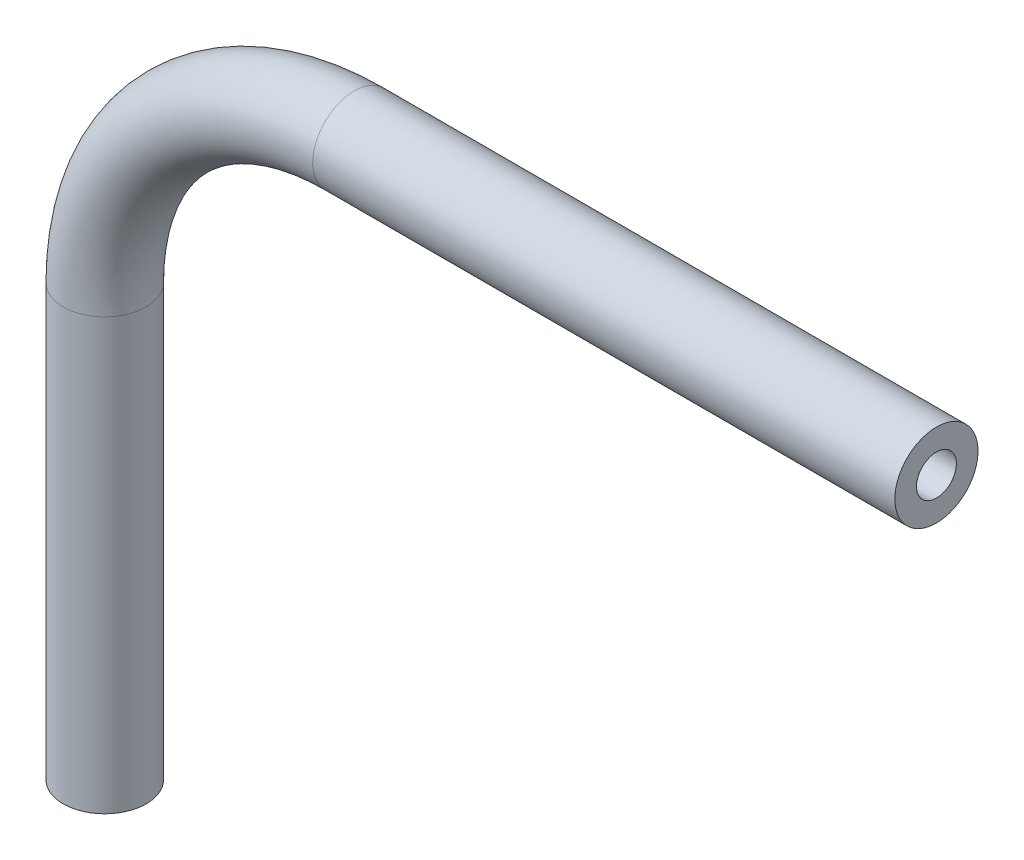
SolidWorks part; units mm, degrees
material "AISI Type 316L stainless steel"
ref_plane "Front Plane" through (0, 0, 0) normal (0, 0, 1) x (1, 0, 0)
ref_plane "Top Plane" through (0, 0, 0) normal (0, 1, 0) x (1, 0, 0)
ref_plane "Right Plane" through (0, 0, 0) normal (1, 0, 0) x (0, 0, -1)
sketch "Sketch1" plane through (0, 0, 0) normal (0, 0, 1) x (1, 0, 0)
  line L0 (0, -34.3808) -> (0, -1.5223)
  line L1 (19.05, 17.5277) -> (63.5, 17.5277)
  arc A0 (0, -1.5223) -> (19.05, 17.5277) centre (19.05, -1.5223) cw
  point P6 (0, 17.5277)
  dimension "D3" = 19.05
  dimension "D1" = 63.5
  dimension "D2" = 51.9085
  dimension "D4" = 90
ref_plane "Plane1" through (63.5, 17.5277, 0) normal (1, 0, 0) x (0, 0, -1)
sketch "Sketch2" plane through (63.5, 17.5277, 0) normal (1, 0, 0) x (0, 0, -1)
  circle A0 centre (0, 0) radius 3.175
  circle A1 centre (0, 0) radius 1.524
  dimension "D1" = 6.35
  dimension "D2" = 3.048
sweep "Sweep1" add profiles "Sketch2" path "Sketch1"
